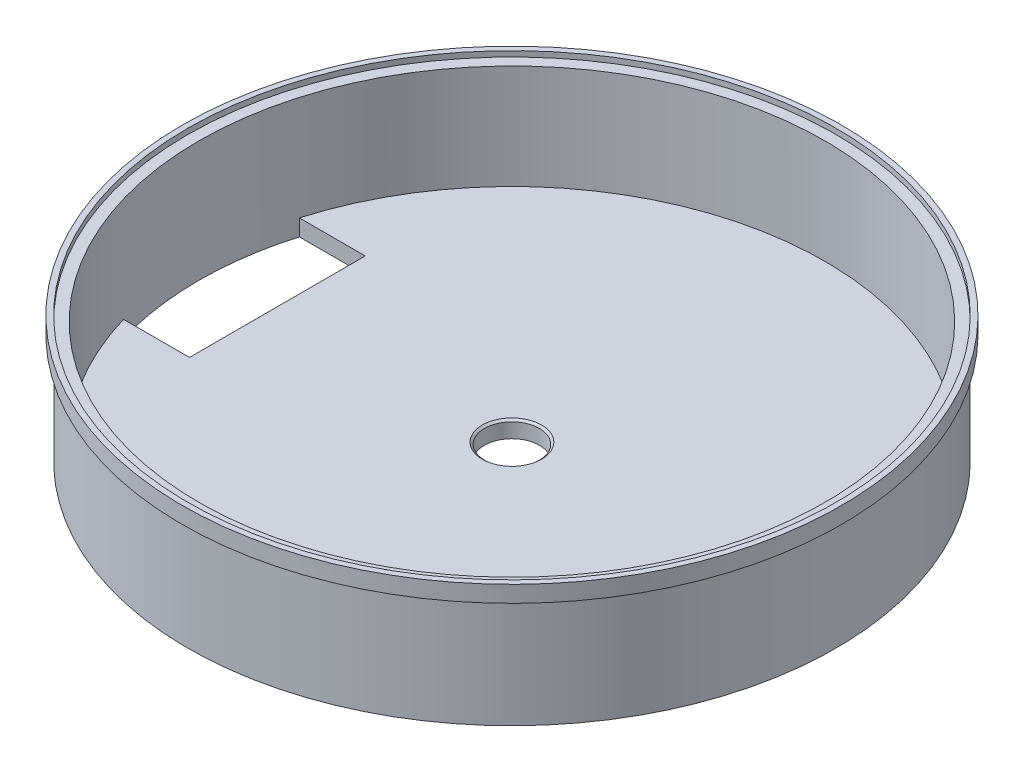
SolidWorks part; units mm, degrees
ref_plane "Front Plane" through (0, 0, 0) normal (0, 0, 1) x (1, 0, 0)
ref_plane "Top Plane" through (0, 0, 0) normal (0, 1, 0) x (1, 0, 0)
ref_plane "Right Plane" through (0, 0, 0) normal (1, 0, 0) x (0, 0, -1)
sketch "Sketch1" plane through (0, 0, 0) normal (0, 0, 1) x (1, 0, 0)
  line L0 (0, 0) -> (0, 8.9331) construction
  line L1 (0, 0) -> (0, -31.3195) construction
  line L2 (-95.25, 5.193) -> (-95.25, 0.4305)
  line L3 (-95.25, 0.4305) -> (-93.6625, 0.4305)
  line L7 (-93.6625, 0.4305) -> (-93.6625, -31.3195)
  line L8 (-93.6625, -31.3195) -> (0, -31.3195)
  line L9 (0, -31.3195) -> (0, -26.557)
  line L10 (0, -26.557) -> (-90.4875, -26.557)
  line L11 (-90.4875, -26.557) -> (-90.4875, 3.6055)
  line L12 (-90.4875, 3.6055) -> (-93.6625, 3.6055)
  line L13 (-93.6625, 3.6055) -> (-93.6625, 5.193)
  line L14 (-93.6625, 5.193) -> (-95.25, 5.193)
  point P7 (-15.9557, 0.5919)
  dimension "D1" = 4.7625
  dimension "D2" = 1.5875
  dimension "D3" = 95.25
  dimension "D4" = 31.75
  dimension "D5" = 4.7625
  dimension "D6" = 3.175
  dimension "D7" = 1.5875
  dimension "D8" = 1.5875
revolve "Revolve1" add sketch "Sketch1" angle 360 about L1
sketch "Sketch4" plane through (0, -26.557, 0) normal (0, 1, 0) x (1, 0, 0)
  point P0 (0, 0)
hole_wizard "5/8 (0.625) Diameter Hole1" positions "Sketch5" profile "Sketch7" hole size "5/8" standard "ANSI Inch" end condition through all
sketch "Sketch5" plane through (0, -26.557, 0) normal (0, 1, 0) x (1, 0, 0)
  point P0 (0, 0)
sketch "Sketch7" plane through (0, -26.557, 0) normal (1, 0, 0) x (0, 0, 1)
  line L0 (0, 0) -> (0, 4.7625)
  line L1 (0, 4.7625) -> (7.9375, 4.7625)
  line L2 (7.9375, 4.7625) -> (7.9375, 0.5328)
  line L3 (7.9375, 0.5328) -> (8.5725, 0)
  line L5 (8.5725, 0) -> (0, 0)
  line L6 (-7.9375, 0.5328) -> (-8.5725, 0) construction
  line L11 (0, -6.35) -> (0, 107.95) construction
  dimension "Thru Hole Dia." = 15.875
  dimension "Thru Hole Depth" = 4.7625
  dimension "Near C'Sink Dia." = 17.145
  dimension "Near C'Sink Angle" = 100
sketch "Sketch12" plane through (0, -26.557, 0) normal (0, 1, 0) x (1, 0, 0)
  line L0 (-86.8495, 25.4) -> (-67.7995, 25.4)
  line L1 (-67.7995, 25.4) -> (-67.7995, -25.4)
  line L2 (-67.7995, -25.4) -> (-86.8495, -25.4)
  circle A0 centre (0, 0) radius 90.4875 construction
  circle A1 centre (0, 0) radius 90.4875 construction
  arc A2 (-86.8495, 25.4) -> (-86.8495, -25.4) centre (0, 0) ccw
  dimension "D1" = 19.05
  dimension "D2" = 50.8
extrude "Cut-Extrude1" cut sketch "Sketch12" against normal blind 25.4
